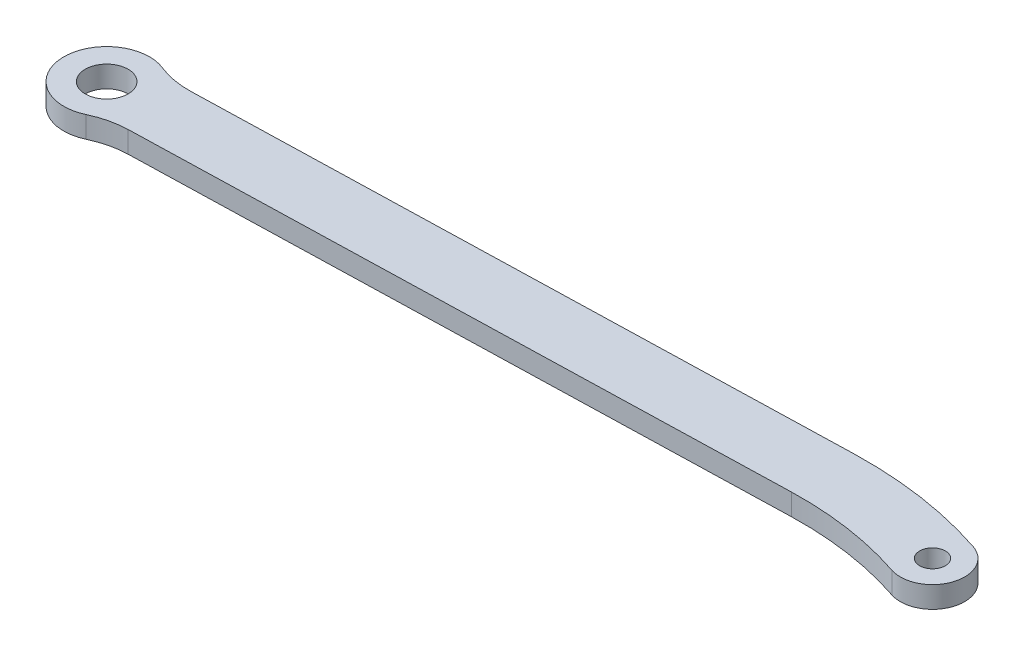
SolidWorks part; units mm, degrees
ref_plane "Front Plane" through (0, 0, 0) normal (0, 0, 1) x (1, 0, 0)
ref_plane "Top Plane" through (0, 0, 0) normal (0, 1, 0) x (1, 0, 0)
ref_plane "Right Plane" through (0, 0, 0) normal (1, 0, 0) x (0, 0, -1)
sketch "Sketch1" plane through (0, 0, 0) normal (0, 1, 0) x (1, 0, 0)
  line L0 (-61.1187, 0) -> (61.1187, 0) construction
  line L1 (-61.2493, 4.7607) -> (41.9, 7.5893)
  line L2 (-60.9882, -4.7607) -> (42.1611, -1.9321)
  line L3 (42.1611, -1.9321) -> (43.5536, -52.713) construction
  line L4 (43.5536, -52.713) -> (59.6132, -4.5183) construction
  line L5 (66.6537, 25.6572) -> (-52.8613, 0.0022) construction
  arc A0 (-61.2493, 4.7607) -> (-60.9882, -4.7607) centre (-61.1187, 0) ccw
  arc A1 (62.6243, 4.5183) -> (59.6132, -4.5183) centre (61.1187, 0) cw
  arc A2 (42.1611, -1.9321) -> (59.6132, -4.5183) centre (43.5536, -52.713) cw
  arc A3 (41.9, 7.5893) -> (62.6243, 4.5183) centre (43.5536, -52.713) cw
  circle A4 centre (-61.1187, 0) radius 3.175
  circle A5 centre (61.1187, 0) radius 1.905
  circle A6 centre (-61.1187, 0) radius 6.35
  point P8 (0, 0)
  dimension "D1" = 4.7625
  dimension "D2" = 3.81
  dimension "D3" = 50.8
  dimension "D4" = 6.35
  dimension "D6" = 12.7
  dimension "D5" = 20
extrude "Boss-Extrude1" add sketch "Sketch1" along normal blind 3.175 contours A6 L2 A2 A1 A3 L1 A5 | L2 A6 L1 A0 A4
fillet "Fillet1" radius 12.7 2 edges at (-56.7896, 1.5875, 4.6456) (-57.0507, 1.5875, -4.8758)
